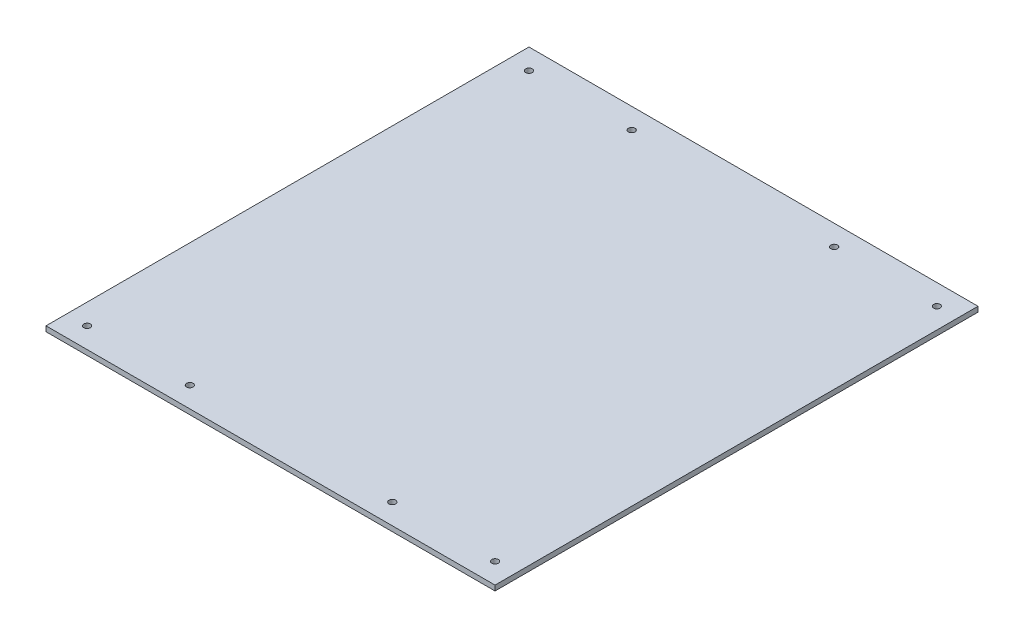
SolidWorks part; units mm, degrees
ref_plane "Front Plane" through (0, 0, 0) normal (0, 0, 1) x (1, 0, 0)
ref_plane "Top Plane" through (0, 0, 0) normal (0, 1, 0) x (1, 0, 0)
ref_plane "Right Plane" through (0, 0, 0) normal (1, 0, 0) x (0, 0, -1)
sketch "Sketch1" plane through (0, 0, 0) normal (0, 1, 0) x (1, 0, 0)
  line L1 (-218.5, -235) -> (218.5, -235)
  line L2 (-218.5, -235) -> (-218.5, 235)
  line L3 (-218.5, 235) -> (218.5, 235)
  line L4 (218.5, -235) -> (218.5, 235)
  line L5 (-218.5, -235) -> (218.5, 235) construction
  line L6 (-218.5, 235) -> (218.5, -235) construction
  point P0 (0, 0)
  dimension "D1" = 437
  dimension "D2" = 470
extrude "Boss-Extrude1" add sketch "Sketch1" along normal blind 5
hole_wizard "M6 Clearance Hole1" positions "Sketch3" profile "Sketch2" hole size "M6" standard "ANSI Metric"
sketch "Sketch3" plane through (0, 5, 0) normal (0, 1, 0) x (1, 0, 0)
  line L0 (-1089.4391, -215) -> (48910.5609, -215) construction
  line L1 (-1065.6521, 215) -> (48934.3479, 215) construction
  line L2 (-198.5, -977.1645) -> (-198.5, 49022.8355) construction
  line L3 (-98.5, -976.213) -> (-98.5, 49023.787) construction
  line L4 (98.5, -978.116) -> (98.5, 49021.884) construction
  line L5 (198.5, -979.0674) -> (198.5, 49020.9326) construction
  line L6 (-218.5, -235) -> (218.5, -235) construction
  line L7 (218.5, 235) -> (-218.5, 235) construction
  line L8 (-218.5, 235) -> (-218.5, -235) construction
  line L9 (218.5, -235) -> (218.5, 235) construction
  point P46 (-198.5, 215)
  point P47 (-98.5, 215)
  point P49 (98.5, 215)
  point P51 (198.5, 215)
  point P53 (-198.5, -215)
  point P55 (-98.5, -215)
  point P57 (98.5, -215)
  point P59 (198.5, -215)
  dimension "D1" = 20
  dimension "D2" = 20
  dimension "D3" = 20
  dimension "D4" = 20
  dimension "D5" = 100
  dimension "D6" = 100
sketch "Sketch2" plane through (-198.5, 5, -215) normal (1, 0, 0) x (0, 0, 1)
  line L0 (0, 0) -> (0, 11.9228)
  line L1 (0, 11.9228) -> (3.2, 10)
  line L2 (3.2, 10) -> (3.2, 0)
  line L5 (3.2, 0) -> (0, 0)
  line L10 (0, 11.9228) -> (-3.2, 10) construction
  line L11 (0, -6.35) -> (0, 107.95) construction
  dimension "Hole Dia." = 6.4
  dimension "Hole Depth" = 10
  dimension "Drill Angle" = 118
